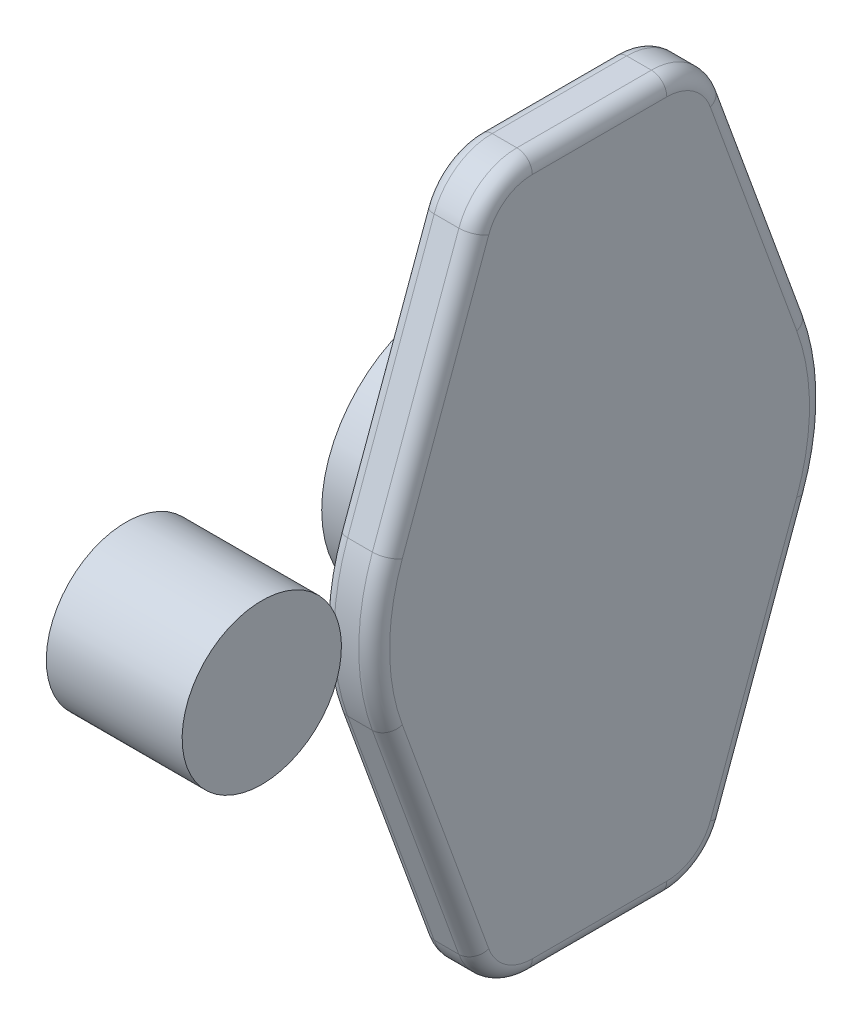
SolidWorks part; units mm, degrees
ref_plane "Front Plane" through (0, 0, 0) normal (0, 0, 1) x (1, 0, 0)
ref_plane "Top Plane" through (0, 0, 0) normal (0, 1, 0) x (1, 0, 0)
ref_plane "Right Plane" through (0, 0, 0) normal (1, 0, 0) x (0, 0, -1)
sketch "Sketch1" plane through (0, 0, 0) normal (0, 0, 1) x (1, 0, 0)
  line L0 (8.255, 0) -> (-8.255, 0) construction
  line L1 (30.255, 0) -> (-30.255, 0) construction
  line L2 (8.255, 0) -> (8.255, 12.9)
  line L3 (8.255, 12.9) -> (30.255, 12.9)
  line L4 (30.255, 12.9) -> (30.255, 0)
  line L5 (8.255, 0) -> (30.255, 0)
  point P4 (0, 0)
  point P8 (0, 0)
  dimension "D1" = 22
  dimension "D2" = 16.51
  dimension "D3" = 12.9
revolve "Revolve1" add sketch "Sketch1" angle 360 about L5
sketch "Sketch2" plane through (8.255, 0, 0) normal (-1, 0, 0) x (0, 0, 1)
  circle A0 centre (0, 0) radius 3.7138
  dimension "D1" = 7.4275
extrude "Cut-Extrude1" cut sketch "Sketch2" against normal blind 7.5725
sketch "Sketch3" plane through (30.255, 0, 0) normal (1, 0, 0) x (0, 0, -1)
  line L0 (-20.8953, -55) -> (-20.8953, -46.1532)
  line L1 (13.175, -55) -> (-13.175, -55) construction
  line L2 (13.175, -55) -> (13.175, 55) construction
  line L3 (13.175, 55) -> (-13.175, 55) construction
  line L4 (-13.175, -55) -> (-13.175, 55) construction
  line L5 (13.175, -55) -> (-13.175, 55) construction
  line L6 (13.175, 55) -> (-13.175, -55) construction
  line L7 (-24.3823, -32.1152) -> (-32.3245, -17.1152)
  line L9 (-5.4548, -55) -> (-5.4548, -44)
  line L11 (5.4547, -44) -> (5.4547, -55)
  line L12 (20.8953, -55) -> (20.8953, -46.1532)
  line L13 (24.3823, -32.1152) -> (32.3245, -17.1152)
  line L14 (14.3, 0) -> (-14.3, 0) construction
  line L15 (13.175, -55) -> (-13.175, 55) construction
  line L16 (13.175, 55) -> (-13.175, -55) construction
  line L17 (13.175, 55) -> (-13.175, 55) construction
  line L18 (24.3823, 32.1152) -> (32.3245, 17.1152)
  line L19 (20.8953, 55) -> (20.8953, 46.1532)
  line L20 (5.4547, 44) -> (5.4547, 55)
  line L21 (-5.4548, 55) -> (-5.4548, 44)
  line L22 (-24.3823, 32.1152) -> (-32.3245, 17.1152)
  line L23 (-20.8953, 55) -> (-20.8953, 46.1532)
  arc A15 (32.3245, -17.1152) -> (32.3245, 17.1152) centre (0, 0) ccw
  arc A16 (-5.4548, 55) -> (-20.8953, 55) centre (-13.175, 55) ccw
  arc A17 (-20.8953, -55) -> (-5.4548, -55) centre (-13.175, -55) ccw
  arc A18 (5.4547, -55) -> (20.8953, -55) centre (13.175, -55) ccw
  arc A19 (20.8953, 55) -> (5.4547, 55) centre (13.175, 55) ccw
  arc A20 (-5.4548, -44) -> (5.4547, -44) centre (0, -44) cw
  arc A21 (20.8953, -46.1532) -> (24.3823, -32.1152) centre (50.8953, -46.1532) cw
  arc A22 (-20.8953, -46.1532) -> (-24.3823, -32.1152) centre (-50.8953, -46.1532) ccw
  arc A23 (-20.8953, 46.1532) -> (-24.3823, 32.1152) centre (-50.8953, 46.1532) cw
  arc A24 (20.8953, 46.1532) -> (24.3823, 32.1152) centre (50.8953, 46.1532) ccw
  arc A25 (-5.4548, 44) -> (5.4547, 44) centre (0, 44) ccw
  arc A26 (5.4547, 55) -> (20.8953, 55) centre (13.175, 55) cw
  arc A27 (-20.8953, 55) -> (-5.4548, 55) centre (-13.175, 55) cw
  arc A29 (-32.3245, 17.1152) -> (-32.3245, -17.1152) centre (0, 0) ccw
  dimension "D3" = 15.4405
  dimension "D5" = 7.7203
  dimension "D4" = 30
  dimension "D7" = 15
  dimension "D9" = 110
  dimension "D1" = 73.152
  dimension "D6" = 15
  dimension "D2" = 26.35
  dimension "D8" = 11
sketch "Sketch4" plane through (30.255, 0, 0) normal (1, 0, 0) x (0, 0, -1)
  circle A0 centre (0, 0) radius 3.7138
  dimension "D1" = 7.4275
extrude "Cut-Extrude2" [suppressed] cut sketch "Sketch4" against normal blind 7.0725
move or copy body "Body-Move/Copy1" bodies to move or copy 102 copy yes number of copies 1 translate (0, 0, 50.4528)
sketch "Sketch5" plane through (0, 0, 0) normal (0, 0, 1) x (1, 0, 0)
  line L0 (8.255, 0) -> (34.255, 0) construction
  line L1 (8.255, 12.9) -> (8.255, -12.9) construction
  line L2 (34.255, 0) -> (25.755, 0) construction
  line L3 (34.255, 0) -> (34.255, 47.5)
  line L4 (34.255, 47.5) -> (25.755, 47.5)
  line L5 (25.755, 47.5) -> (25.755, 0)
  line L6 (34.255, 0) -> (25.755, 0)
  dimension "D1" = 26
  dimension "D2" = 8.5
  dimension "D3" = 47.5
sketch "Sketch6" plane through (30.255, 0, 0) normal (1, 0, 0) x (0, 0, -1)
  line L1 (10.8915, -57.5) -> (-10.8915, -57.5)
  line L3 (10.8915, 57.5) -> (-10.8915, 57.5)
  line L5 (-34.2929, 12.5) -> (-20.2868, 50.9247)
  line L6 (-34.2929, -12.5) -> (-20.2868, -50.9247)
  line L9 (0, 0) -> (-36.5, 0) construction
  line L10 (0, -57.5) -> (0, 57.5) construction
  line L15 (34.2929, -12.5) -> (20.2868, -50.9247)
  line L16 (34.2929, 12.5) -> (20.2868, 50.9247)
  arc A0 (-34.2929, 12.5) -> (-34.2929, -12.5) centre (0, 0) ccw
  arc A1 (-20.2868, 50.9247) -> (-10.8915, 57.5) centre (-10.8915, 47.5) cw
  arc A2 (-20.2868, -50.9247) -> (-10.8915, -57.5) centre (-10.8915, -47.5) ccw
  arc A3 (20.2868, -50.9247) -> (10.8915, -57.5) centre (10.8915, -47.5) cw
  arc A4 (20.2868, 50.9247) -> (10.8915, 57.5) centre (10.8915, 47.5) ccw
  arc A5 (34.2929, -12.5) -> (34.2929, 12.5) centre (0, 0) ccw
  point P0 (0, 0)
  point P16 (0, 0)
  dimension "D2" = 73
  dimension "D3" = 10
  dimension "D8" = 10
  dimension "D1" = 115
  dimension "D6" = 25
  dimension "D7" = 12.5
extrude "Boss-Extrude1" add sketch "Sketch6" along normal mid plane 8.5
fillet "Fillet3" radius 2.5 12 edges at (34.505, -55.6929, -16.6253) (34.505, -57.5, 0) (34.505, -55.6929, 16.6253) (34.505, -31.7123, 27.2898) (34.505, 0, 36.5) (34.505, 31.7123, 27.2898) (34.505, 55.6929, 16.6253) (34.505, 57.5, 0) (34.505, 55.6929, -16.6253) (34.505, 31.7123, -27.2898) (34.505, 0, -36.5) (34.505, -31.7123, -27.2898)
sketch "Sketch8" plane through (26.005, 0, 0) normal (-1, 0, 0) x (0, 0, 1)
  circle A0 centre (0, 0) radius 12.9 construction
  circle A1 centre (0, 0) radius 12.9
  circle A2 centre (0, 0) radius 20
  dimension "D1" = 40
extrude "Boss-Extrude2" add sketch "Sketch8" along normal blind 16.5
fillet "Fillet4" radius 2 13 edges at (26.005, 0, 36.5) (26.005, -31.7123, 27.2898) (26.005, -55.6929, 16.6253) (26.005, -57.5, 0) (26.005, -55.6929, -16.6253) (26.005, -31.7123, -27.2898) (26.005, 0, -36.5) (26.005, 31.7123, -27.2898) (26.005, 55.6929, -16.6253) (26.005, 57.5, 0) (26.005, 55.6929, 16.6253) (26.005, 31.7123, 27.2898) (26.005, 20, 0)
